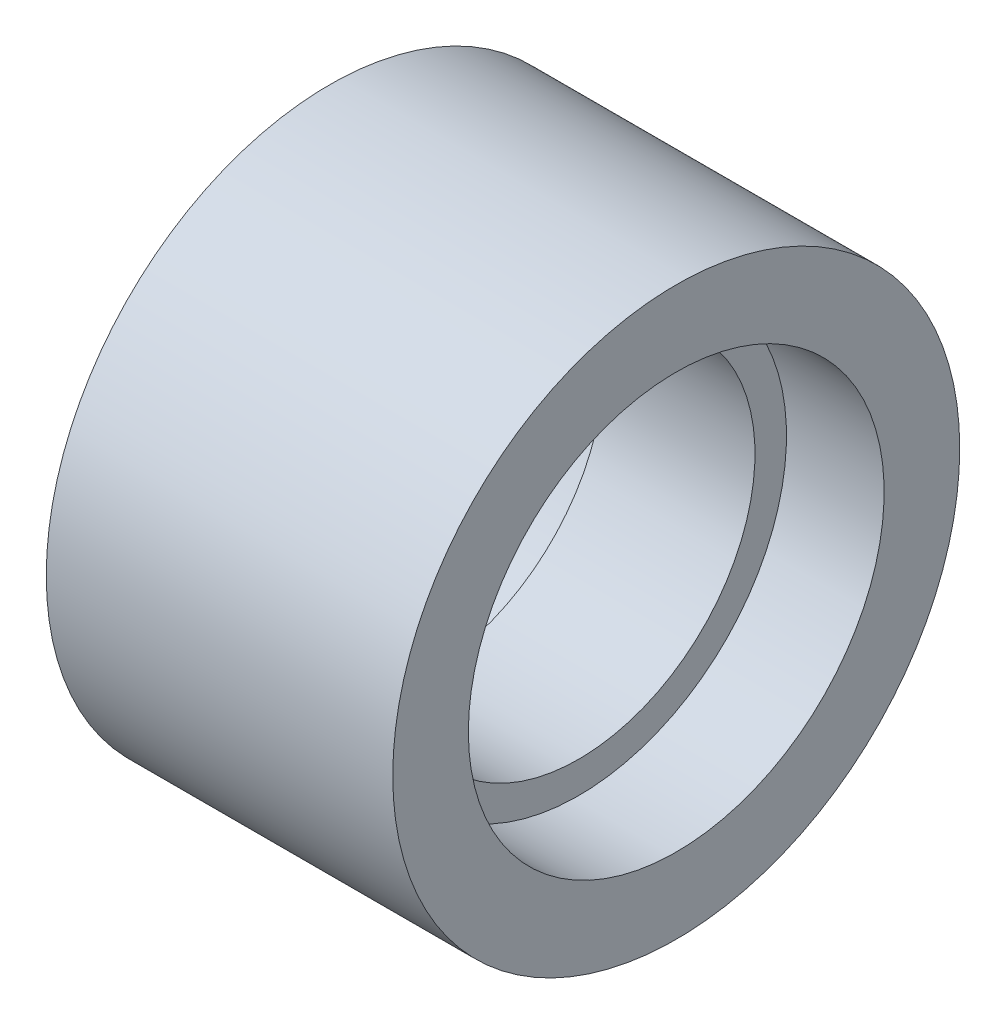
SolidWorks part; units mm, degrees
material "1023 Carbon Steel Sheet (SS)"
ref_plane "Front Plane" through (0, 0, 0) normal (0, 0, 1) x (1, 0, 0)
ref_plane "Top Plane" through (0, 0, 0) normal (0, 1, 0) x (1, 0, 0)
ref_plane "Right Plane" through (0, 0, 0) normal (1, 0, 0) x (0, 0, -1)
sketch "Sketch1" plane through (0, 0, 0) normal (0, 0, 1) x (1, 0, 0)
  line L0 (-9.4444, 0) -> (22.963, 0) construction
  line L2 (-55, 90) -> (55, 90)
  line L3 (-55, 90) -> (-55, 66)
  line L4 (-55, 66) -> (55, 66)
  line L5 (55, 90) -> (55, 66)
  line L6 (-55, 90) -> (55, 66) construction
  line L7 (-55, 66) -> (55, 90) construction
  line L8 (-24, 56) -> (24, 56)
  line L9 (-24, 56) -> (-24, 66)
  line L10 (-24, 66) -> (24, 66)
  line L11 (24, 56) -> (24, 66)
  line L12 (-24, 56) -> (24, 66) construction
  line L13 (-24, 66) -> (24, 56) construction
  text T0 "MADE IN UMIC,IITB"
  point P3 (0, 78)
  point P8 (0, 61)
  dimension "D1" = 10
  dimension "D2" = 66
  dimension "D3" = 90
  dimension "D4" = 110
  dimension "D5" = 48
revolve "Revolve1" add sketch "Sketch1" angle 360 about L0
sketch "Sketch10" plane through (55, 0, 0) normal (1, 0, 0) x (0, 0, -1)
  circle A0 centre (0, 0) radius 70.4828
  text T0 "<b>                                        MADE IN UMIC </b>" font "Yu Gothic" height 15.175
